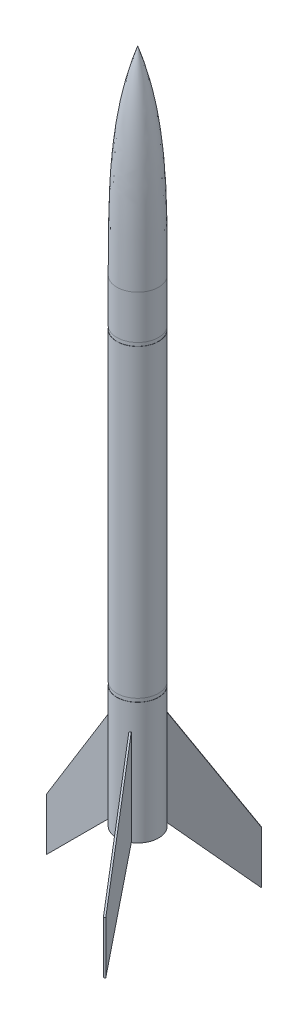
SolidWorks part; units mm, degrees
material "Corrugated Paper"
ref_plane "Front Plane" through (0, 0, 0) normal (0, 0, 1) x (1, 0, 0)
ref_plane "Top Plane" through (0, 0, 0) normal (0, 1, 0) x (1, 0, 0)
ref_plane "Right Plane" through (0, 0, 0) normal (1, 0, 0) x (0, 0, -1)
sketch "Sketch1" plane through (0, 0, 0) normal (0, 0, 1) x (1, 0, 0)
  line L0 (0, 0) -> (0, 388)
  line L1 (12, 274) -> (12, 0)
  line L2 (12, 0) -> (0, 0)
  line L3 (0, 0) -> (0, 485.1034) construction
  spline S0 degree 3 poles (0, 388) (12, 353.4637) (12, 313.5392) (12, 274.9121) (12, 274) knots 0 0 0 0 0.976387 1 1 1 1
  dimension "D1" = 24
  dimension "D4" = 55
  dimension "D2" = 388
  dimension "D3" = 274
revolve "Revolve1" add sketch "Sketch1" angle 360 about L3
sketch "Sketch2" plane through (0, 0, 0) normal (0, 0, 1) x (1, 0, 0)
  line L0 (-12, 0) -> (-52, -40)
  line L1 (-52, -40) -> (-52, -10)
  line L2 (-52, -10) -> (-12, 55)
  line L3 (-12, 274) -> (-12, 0) construction
  line L5 (-12, 0) -> (-9, 0)
  line L6 (-12, 0) -> (12, 0) construction
  line L7 (-9, 0) -> (-9, 55)
  line L8 (-9, 55) -> (-12, 55)
  dimension "D1" = 30
  dimension "D2" = 55
  dimension "D3" = 40
  dimension "D4" = 40
  dimension "D5" = 3
extrude "Boss-Extrude1" add sketch "Sketch2" along normal mid plane 1
pattern_circular "CirPattern10" count 3 over 360 about axis through (0, 0, 0) along (0, 1, 0) of "Boss-Extrude1"
sketch "Sketch4" plane through (0, 0, 0) normal (0, 0, 1) x (1, 0, 0)
  line L0 (12, 0) -> (12, 274) construction
  line L1 (12, 72) -> (11.9, 72)
  line L2 (12, 72) -> (12, 70)
  line L3 (12, 70) -> (11.9, 70)
  line L4 (11.9, 72) -> (11.9, 70)
  line L5 (-11.9896, 0) -> (5.5618, 0) construction
  line L7 (12, 249) -> (11.9, 249)
  line L8 (12, 249) -> (12, 247)
  line L9 (12, 247) -> (11.9, 247)
  line L10 (11.9, 249) -> (11.9, 247)
  dimension "D1" = 0.1
  dimension "D2" = 2
  dimension "D3" = 72
  dimension "D4" = 2
  dimension "D5" = 0.1
  dimension "D6" = 247
revolve "Cut-Revolve1" cut sketch "Sketch4" angle 360 about axis through (0, 0, 0) along (0, -1, 0)
